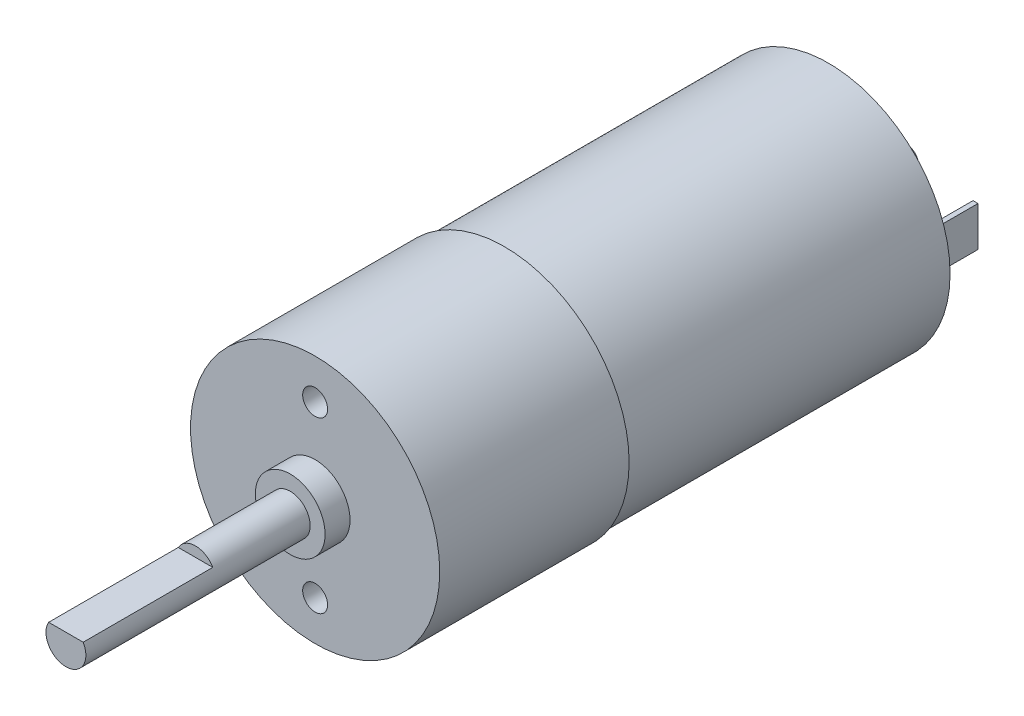
SolidWorks part; units mm, degrees
ref_plane "Front Plane" through (0, 0, 0) normal (0, 0, 1) x (1, 0, 0)
ref_plane "Top Plane" through (0, 0, 0) normal (0, 1, 0) x (1, 0, 0)
ref_plane "Right Plane" through (0, 0, 0) normal (1, 0, 0) x (0, 0, -1)
sketch "스케치1" plane through (0, 0, 0) normal (0, 0, 1) x (1, 0, 0)
  circle A0 centre (0, 0) radius 12.5
  dimension "D1" = 25
extrude "보스-돌출1" add sketch "스케치1" along normal blind 19
sketch "스케치2" plane through (0, 0, 19) normal (0, 0, 1) x (1, 0, 0)
  circle A0 centre (0, 0) radius 3.5
extrude "보스-돌출2" add sketch "스케치2" along normal blind 2.5
sketch "스케치3" plane through (0, 0, 21.5) normal (0, 0, 1) x (1, 0, 0)
  circle A0 centre (0, 0) radius 2
extrude "보스-돌출3" add sketch "스케치3" along normal blind 22.5
sketch "스케치4" plane through (0, 0, 44) normal (0, 0, 1) x (1, 0, 0)
  line L0 (0, 0) -> (50000, 0) construction
  line L1 (-2.3599, 1) -> (49997.6401, 1) construction
  line L3 (3.3297, 1) -> (-3.2328, 1)
  line L4 (3.3297, 1) -> (3.3297, 2.1821)
  line L5 (3.3297, 2.1821) -> (-3.2328, 2.1821)
  line L6 (-3.2328, 1) -> (-3.2328, 2.1821)
  dimension "D1" = 1
extrude "컷-돌출1" cut sketch "스케치4" against normal blind 13
sketch "스케치5" plane through (0, 0, 0) normal (0, 0, -1) x (-1, 0, 0)
  circle A0 centre (0, 0) radius 12.2
  dimension "D1" = 24.4
extrude "보스-돌출5" add sketch "스케치5" along normal blind 32.5
sketch "스케치6" plane through (0, 0, -32.5) normal (0, 0, -1) x (-1, 0, 0)
  circle A0 centre (0, 0) radius 3.5
extrude "보스-돌출6" add sketch "스케치6" along normal blind 3
sketch "스케치7" plane through (0, 0, -35.5) normal (0, 0, -1) x (-1, 0, 0)
  circle A0 centre (0, 0) radius 1
extrude "보스-돌출7" add sketch "스케치7" along normal blind 5
sketch "스케치8" plane through (0, 0, 19) normal (0, 0, 1) x (1, 0, 0)
  line L0 (0, 0.6304) -> (0, 50000.6304) construction
  circle A0 centre (0, 0) radius 8.5 construction
  circle A1 centre (0, 8.5) radius 1.25
  circle A2 centre (0, -8.5) radius 1.25
  dimension "D1" = 2.5
  dimension "D2" = 2.5
extrude "컷-돌출2" cut sketch "스케치8" against normal blind 5
sketch "스케치9" plane through (0, 0, -32.5) normal (0, 0, -1) x (-1, 0, 0)
  line L0 (0, 0) -> (50000, 0) construction
  line L1 (-9, 2.2495) -> (-9, -49997.7505) construction
  line L2 (9, 2.6702) -> (9, -49997.3298) construction
  line L4 (-9, -2) -> (-9.5, -2)
  line L5 (-9, -2) -> (-9, 2)
  line L6 (-9, 2) -> (-9.5, 2)
  line L7 (-9.5, -2) -> (-9.5, 2)
  line L8 (9, -2) -> (9.5, -2)
  line L9 (9, -2) -> (9, 2)
  line L10 (9, 2) -> (9.5, 2)
  line L11 (9.5, -2) -> (9.5, 2)
  dimension "D1" = 0.5
  dimension "D2" = 9
  dimension "D3" = 9
  dimension "D4" = 0.5
  dimension "D5" = 4
  dimension "D6" = 4
  dimension "D7" = 2
  dimension "D8" = 2
extrude "보스-돌출8" add sketch "스케치9" along normal blind 5.5
